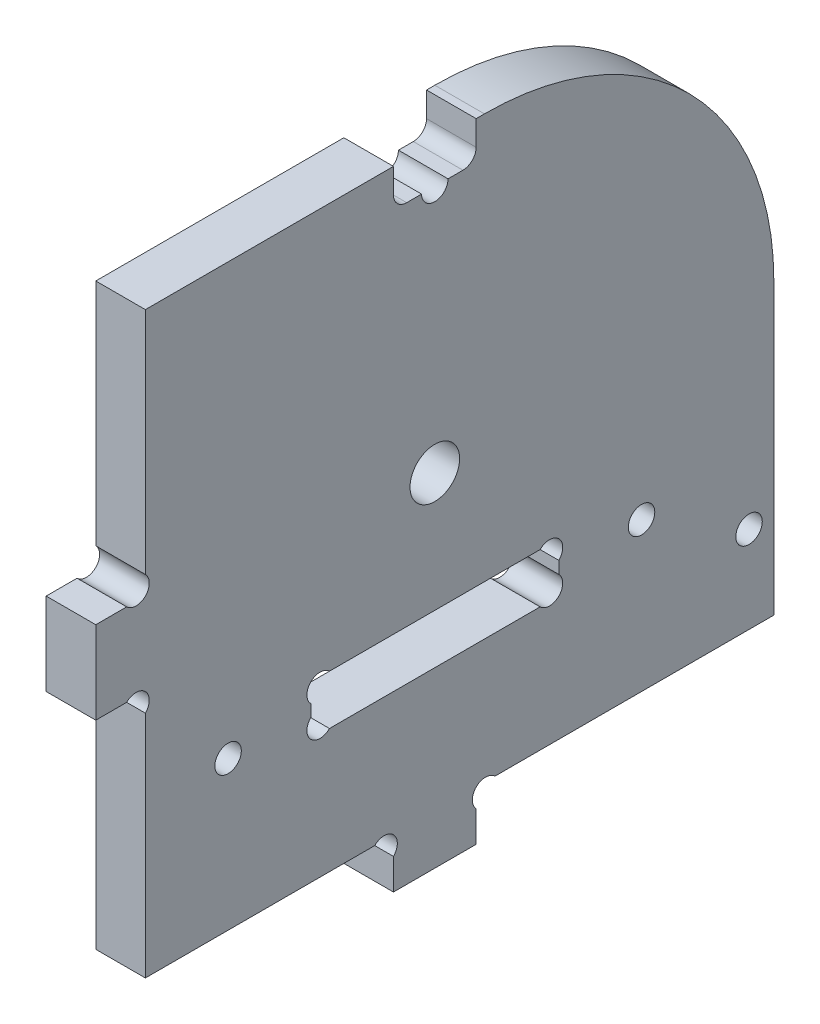
SolidWorks part; units mm, degrees
ref_plane "Plan de face" through (0, 0, 0) normal (0, 0, 1) x (1, 0, 0)
ref_plane "Plan de dessus" through (0, 0, 0) normal (0, 1, 0) x (1, 0, 0)
ref_plane "Plan de droite" through (0, 0, 0) normal (1, 0, 0) x (0, 0, -1)
sketch "Esquisse1" plane through (0, 0, 0) normal (1, 0, 0) x (0, 0, -1)
  line L0 (0, -4.5625) -> (0, 134.1836) construction
  line L1 (-32.3115, 0) -> (104.4265, 0) construction
  line L2 (-24.3695, 6) -> (104.4265, 6) construction
  line L3 (6, -26.2376) -> (6, 112.02) construction
  line L4 (82, -26.2376) -> (82, 134.1836) construction
  line L5 (-26.3115, 76) -> (110.4265, 76) construction
  line L6 (41, 99.8569) -> (41, -16.9546) construction
  line L7 (104.4265, 41.4) -> (32.7277, 41.4) construction
  line L8 (46, 9.2963) -> (46, -16.9546) construction
  line L9 (-8.4142, 41) -> (14.8973, 41) construction
  line L10 (-8.4142, 36) -> (14.8973, 36) construction
  line L11 (6, 36) -> (-7.6399, 22.3601) construction
  line L12 (46, 3.7373) -> (46, 0)
  line L13 (46, 6) -> (62.0517, -10.0517) construction
  line L14 (46, 0) -> (36, 0)
  line L15 (36, 0) -> (36, 3.7373)
  line L16 (3.7373, 36) -> (0, 36)
  line L17 (0, 36) -> (0, 46)
  line L18 (0, 46) -> (3.7373, 46)
  line L19 (33.7373, 6) -> (6, 6)
  line L20 (6, 6) -> (6, 33.7373)
  line L21 (6, 48.2627) -> (6, 76)
  line L22 (6, 76) -> (36, 76)
  line L23 (82, 41) -> (82, 6)
  line L24 (82, 6) -> (48.2627, 6)
  line L25 (33.3786, 27) -> (96.7836, 27) construction
  line L26 (33.3786, 21) -> (90.8453, 21) construction
  line L27 (38.7851, 24) -> (75.9848, 24) construction
  line L28 (56, 37.6455) -> (56, 17.7019) construction
  line L29 (79, 31.9314) -> (79, 11.6517) construction
  line L30 (75.2714, 16.5) -> (90.8453, 16.5) construction
  line L31 (56, 21) -> (45.1559, 31.8441) construction
  line L32 (56, 24.7373) -> (56, 23.2627)
  line L33 (26, 24.7373) -> (26, 23.2627)
  line L34 (28.2627, 21) -> (53.7373, 21)
  line L35 (28.2627, 27) -> (53.7373, 27)
  line L36 (66, 17.7019) -> (66, 37.6455) construction
  line L37 (28.2627, 71.4) -> (69.0741, 71.4) construction
  line L38 (46, 67.443) -> (46, 77.4965) construction
  line L39 (46, 76) -> (46, 73)
  line L40 (36, 76) -> (36, 73)
  line L41 (37.6, 71.4) -> (39.4, 71.4)
  line L42 (42.6, 71.4) -> (44.4, 71.4)
  line L43 (46, 76) -> (47, 76)
  circle A0 centre (41, 41.4) radius 3
  arc A1 (48.2627, 6) -> (46, 3.7373) centre (47.1314, 4.8686) ccw
  arc A2 (33.7373, 6) -> (36, 3.7373) centre (34.8686, 4.8686) cw
  arc A3 (6, 33.7373) -> (3.7373, 36) centre (4.8686, 34.8686) ccw
  arc A4 (6, 48.2627) -> (3.7373, 46) centre (4.8686, 47.1314) cw
  circle A5 centre (79, 16.5) radius 1.6
  arc A6 (53.7373, 21) -> (56, 23.2627) centre (54.8686, 22.1314) ccw
  arc A7 (53.7373, 27) -> (56, 24.7373) centre (54.8686, 25.8686) cw
  arc A8 (28.2627, 27) -> (26, 24.7373) centre (27.1314, 25.8686) ccw
  arc A9 (28.2627, 21) -> (26, 23.2627) centre (27.1314, 22.1314) cw
  circle A10 centre (66, 24) radius 1.6
  circle A11 centre (16, 24) radius 1.6
  arc A12 (47, 76) -> (82, 41) centre (47, 41) cw
  arc A13 (39.4, 71.4) -> (42.6, 71.4) centre (41, 71.4) ccw
  arc A14 (46, 73) -> (44.4, 71.4) centre (44.4, 73) cw
  arc A15 (36, 73) -> (37.6, 71.4) centre (37.6, 73) ccw
  point P85 (82, 76)
  point P95 (46, 71.4)
  point P102 (36, 71.4)
  dimension "D7" = 35
  dimension "D12" = 21
  dimension "D14" = 15
  dimension "D13" = 3
  dimension "D3" = 6
  dimension "D17" = 45
  dimension "D18" = 10
  dimension "D19" = 35
  dimension "D22" = 1.6
  dimension "D1" = 6
  dimension "D2" = 6
  dimension "D4" = 76
  dimension "D5" = 41
  dimension "D6" = 35.4
  dimension "D8" = 5
  dimension "D9" = 45
  dimension "D10" = 5
  dimension "D11" = 45
  dimension "D15" = 10.5
  dimension "D16" = 3
  dimension "D20" = 4.6
  dimension "D21" = 5
extrude "Boss.-Extru.1" add sketch "Esquisse1" along normal blind 6
